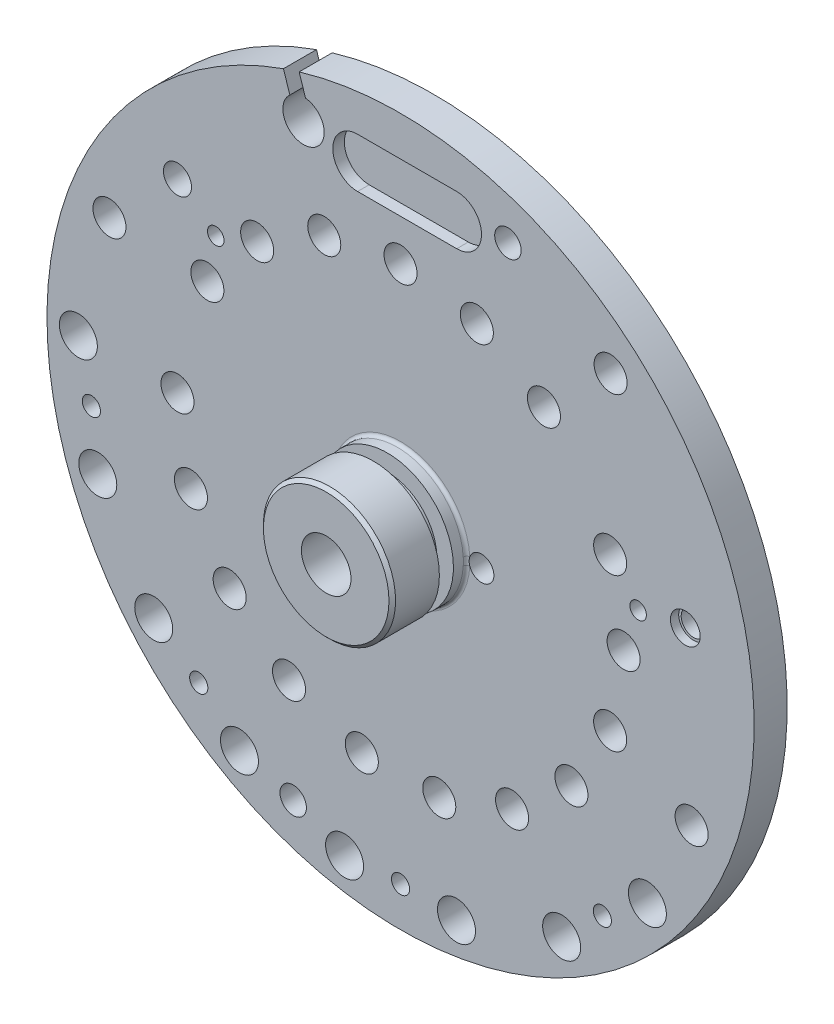
SolidWorks part; units mm, degrees
ref_plane "Front Plane" through (0, 0, 0) normal (0, 0, 1) x (1, 0, 0)
ref_plane "Top Plane" through (0, 0, 0) normal (0, 1, 0) x (1, 0, 0)
ref_plane "Right Plane" through (0, 0, 0) normal (1, 0, 0) x (0, 0, -1)
sketch "Sketch1" plane through (0, 0, 0) normal (0, 0, 1) x (1, 0, 0)
  circle A0 centre (0, 0) radius 21.4
  dimension "D1" = 42.8
extrude "Boss-Extrude1" add sketch "Sketch1" against normal blind 2
sketch "Sketch2" plane through (0, 0, -2) normal (0, 0, -1) x (-1, 0, 0)
  circle A0 centre (0, 0) radius 6.5
  dimension "D1" = 13
extrude "Boss-Extrude2" add sketch "Sketch2" along normal blind 4.7
sketch "Sketch3" plane through (0, 0, 0) normal (0, 0, 1) x (1, 0, 0)
  circle A0 centre (0, 0) radius 4
  dimension "D1" = 8
extrude "Boss-Extrude3" add sketch "Sketch3" along normal offset from surface (4.5 mm away) 6.5 up to face at (6.5, 0, -2)
sketch "Sketch5" plane through (0, 0, -6.7) normal (0, 0, -1) x (-1, 0, 0)
  circle A0 centre (0, 0) radius 3.25
  dimension "D1" = 6.5
extrude "Cut-Extrude2" cut sketch "Sketch5" against normal blind 5.2
sketch "Sketch4" plane through (0, 0, 4.5) normal (0, 0, 1) x (1, 0, 0)
  circle A0 centre (0, 0) radius 1.5
  dimension "D1" = 3
extrude "Cut-Extrude1" cut sketch "Sketch4" against normal up to next
sketch "Sketch6" plane through (0, 0, 0) normal (1, 0, 0) x (0, 0, -1)
  line L0 (-4.5, 0) -> (6.7, 0) construction
  line L1 (-4.5, 4) -> (-4.5, -4) construction
  line L2 (6.7, -6.5) -> (6.7, 6.5) construction
  line L3 (0, 4) -> (-4.5, 4) construction
  line L4 (-1.65, 4) -> (-0.8, 4)
  line L5 (-1.65, 4) -> (-1.65, 3)
  line L6 (-1.65, 3) -> (-0.8, 3)
  line L7 (-0.8, 4) -> (-0.8, 3)
  line L8 (2, -21.4) -> (2, 21.4) construction
  dimension "D1" = 2.8
  dimension "D2" = 0.85
  dimension "D3" = 6
revolve "Cut-Revolve1" cut sketch "Sketch6" angle 360 about L0
sketch "Sketch7" plane through (0, 0, 0) normal (1, 0, 0) x (0, 0, -1)
  line L0 (0, 0) -> (8.4065, 0) construction
  line L1 (6.7, -6.5) -> (6.7, 6.5) construction
  line L2 (6.7, 2.75) -> (6.2, 2.75)
  line L3 (6.7, 2.75) -> (6.7, -2.75)
  line L4 (6.7, -2.75) -> (6.2, -2.75)
  line L5 (6.2, 2.75) -> (6.2, -2.75)
  line L6 (2, -21.4) -> (2, 21.4) construction
  dimension "D1" = 4.2
  dimension "D2" = 5.5
extrude "Cut-Extrude3" cut sketch "Sketch7" against normal through all both and the other way through all
sketch "Sketch8" plane through (0, 0, 0) normal (0, 0, 1) x (1, 0, 0)
  line L0 (0, 0) -> (0, 21.4) construction
  line L1 (-2.6, 17.5) -> (3.4, 17.5) construction
  line L2 (-2.6, 19) -> (3.4, 19)
  line L3 (-2.6, 16) -> (3.4, 16)
  circle A0 centre (0, 0) radius 21.4 construction
  arc A1 (-2.6, 19) -> (-2.6, 16) centre (-2.6, 17.5) ccw
  arc A2 (3.4, 16) -> (3.4, 19) centre (3.4, 17.5) ccw
  circle A3 centre (0, 0) radius 4 construction
  point P7 (0.4, 17.5)
  dimension "D3" = 3
  dimension "D4" = 16
  dimension "D2" = 9
  dimension "D1" = 4.1
extrude "Cut-Extrude4" cut sketch "Sketch8" against normal blind 0.7
hole_wizard "Ø2.0 (2) Diameter Hole6" positions "Sketch14" profile "Sketch13" hole size "Ø2.0" standard "DIN" end condition through all
sketch "Sketch14" plane through (0, 0, -2) normal (0, 0, 1) x (1, 0, 0)
  line L7 (0, 0) -> (-21.4, 0) construction
  line L8 (0, 0) -> (-11.6913, 6.75) construction
  line L9 (-8.6776, 10.3416) -> (0, 0) construction
  line L10 (0, 0) -> (-4.6173, 12.6859) construction
  line L11 (4.6173, 12.6859) -> (0, 0) construction
  line L12 (8.6776, 10.3416) -> (0, 0) construction
  line L13 (0, 0) -> (-12.6859, -4.6173) construction
  line L14 (0, 0) -> (-10.3416, -8.6776) construction
  line L15 (-6.75, -11.6913) -> (0, 0) construction
  line L16 (0, 0) -> (-2.3443, -13.2949) construction
  line L17 (0, 0) -> (2.3443, -13.2949) construction
  line L18 (6.75, -11.6913) -> (0, 0) construction
  line L19 (10.3416, -8.6776) -> (0, 0) construction
  line L20 (12.6859, -4.6173) -> (0, 0) construction
  line L21 (0, 0) -> (13.5, 0) construction
  line L22 (12.6859, 4.6173) -> (0, 0) construction
  circle A1 centre (0, 0) radius 13.5 construction
  circle A2 centre (0, 0) radius 21.4 construction
  point P82 (-11.6913, 6.75)
  point P84 (-8.6776, 10.3416)
  point P86 (-4.6173, 12.6859)
  point P88 (4.6173, 12.6859)
  point P100 (0, 13.5)
  point P103 (8.6776, 10.3416)
  point P108 (-12.6859, -4.6173)
  point P110 (-10.3416, -8.6776)
  point P112 (-6.75, -11.6913)
  point P126 (2.3443, -13.2949)
  point P128 (6.75, -11.6913)
  point P130 (10.3416, -8.6776)
  point P132 (12.6859, -4.6173)
  point P145 (13.5, 0)
  point P147 (12.6859, 4.6173)
  point P156 (-13.5, 0)
  point P159 (-2.3443, -13.2949)
  dimension "D1" = 27
  dimension "D2" = 30
  dimension "D4" = 70
  dimension "D5" = 110
  dimension "D6" = 130
  dimension "D8" = 40
  dimension "D9" = 60
  dimension "D3" = 50
  dimension "D7" = 20
  dimension "D10" = 80
  dimension "D11" = 100
  dimension "D12" = 120
  dimension "D13" = 20
  dimension "D14" = 20
  dimension "D15" = 20
sketch "Sketch13" plane through (-11.6913, 6.75, -2) normal (1, 0, 0) x (0, 1, 0)
  line L0 (0, 0) -> (0, 6.5)
  line L1 (0, 6.5) -> (1, 6.5)
  line L2 (1, 6.5) -> (1, 0)
  line L5 (1, 0) -> (0, 0)
  line L11 (0, -6.35) -> (0, 107.95) construction
  dimension "Thru Hole Dia." = 2
  dimension "Thru Hole Depth" = 6.5
fillet "Fillet2" radius 1 1 edges at (6.5, 0, -2)
hole_wizard "Ø2.3 (2.3) Diameter Hole1" positions "Sketch20" profile "Sketch19" hole size "Ø2.3" standard "DIN" end condition through all
sketch "Sketch20" plane through (0, 0, -2) normal (0, 0, 1) x (1, 0, 0)
  line L3 (0, 0) -> (-19.5, 0) construction
  line L4 (0, 0) -> (-18.324, -6.6694) construction
  line L5 (0, 0) -> (-14.9379, -12.5344) construction
  line L6 (0, 0) -> (-9.75, -16.8875) construction
  line L7 (0, 0) -> (-3.3861, -19.2038) construction
  line L8 (0, 0) -> (3.3861, -19.2038) construction
  line L9 (0, 0) -> (9.75, -16.8875) construction
  line L10 (0, 0) -> (14.9379, -12.5344) construction
  circle A0 centre (0, 0) radius 19.5 construction
  point P35 (-19.5, 0)
  point P60 (-18.324, -6.6694)
  point P66 (-14.9379, -12.5344)
  point P69 (-9.75, -16.8875)
  point P72 (-3.3861, -19.2038)
  point P75 (3.3861, -19.2038)
  point P78 (9.75, -16.8875)
  point P81 (14.9379, -12.5344)
  dimension "D1" = 39
  dimension "D2" = 20
  dimension "D3" = 20
  dimension "D4" = 20
  dimension "D5" = 20
  dimension "D6" = 20
  dimension "D7" = 20
  dimension "D8" = 20
sketch "Sketch19" plane through (-19.5, 0, -2) normal (1, 0, 0) x (0, 1, 0)
  line L0 (0, 0) -> (0, 6.5)
  line L1 (0, 6.5) -> (1.15, 6.5)
  line L2 (1.15, 6.5) -> (1.15, 0)
  line L5 (1.15, 0) -> (0, 0)
  line L11 (0, -6.35) -> (0, 107.95) construction
  dimension "Thru Hole Dia." = 2.3
  dimension "Thru Hole Depth" = 6.5
hole_wizard "Ø2.0 (2) Diameter Hole8" positions "Sketch23" profile "Sketch21" hole size "Ø2.0" standard "DIN" end condition through all
sketch "Sketch23" plane through (0, 0, -2) normal (0, 0, 1) x (1, 0, 0)
  line L0 (0, 0) -> (-21.4, 0) construction
  line L1 (0, 0) -> (-17.6165, 7.1175) construction
  line L2 (12.7135, 14.1198) -> (0, 0) construction
  line L3 (0, 0) -> (17.6165, -7.1175) construction
  circle A0 centre (0, 0) radius 19 construction
  circle A1 centre (0, 0) radius 21.4 construction
  point P11 (-17.6165, 7.1175)
  point P15 (12.7135, 14.1198)
  point P17 (17.6165, -7.1175)
  dimension "D1" = 22
  dimension "D4" = 38
  dimension "D2" = 132
  dimension "D3" = 202
sketch "Sketch21" plane through (-17.6165, 7.1175, -2) normal (1, 0, 0) x (0, 1, 0)
  line L0 (0, 0) -> (0, 6.5)
  line L1 (0, 6.5) -> (1, 6.5)
  line L2 (1, 6.5) -> (1, 0)
  line L5 (1, 0) -> (0, 0)
  line L11 (0, -6.35) -> (0, 107.95) construction
  dimension "Thru Hole Dia." = 2
  dimension "Thru Hole Depth" = 6.5
hole_wizard "Ø2.5 (2.5) Diameter Hole1" positions "Sketch25" profile "Sketch24" hole size "Ø2.5" standard "DIN" end condition through all
sketch "Sketch25" plane through (0, 0, -2) normal (0, 0, 1) x (1, 0, 0)
  line L0 (0, 0) -> (-21.4, 0) construction
  line L1 (-5.8713, 18.0701) -> (0, 0) construction
  line L2 (0, 0) -> (-17.6165, 7.1175) construction
  circle A0 centre (0, 0) radius 19 construction
  circle A1 centre (0, 0) radius 21.4 construction
  point P4 (-5.8713, 18.0701)
  dimension "D1" = 72
sketch "Sketch24" plane through (-5.8713, 18.0701, -2) normal (1, 0, 0) x (0, 1, 0)
  line L0 (0, 0) -> (0, 6.5)
  line L1 (0, 6.5) -> (1.25, 6.5)
  line L2 (1.25, 6.5) -> (1.25, 0)
  line L5 (1.25, 0) -> (0, 0)
  line L11 (0, -6.35) -> (0, 107.95) construction
  dimension "Thru Hole Dia." = 2.5
  dimension "Thru Hole Depth" = 6.5
hole_wizard "Ø1.0 (1) Diameter Hole1" positions "Sketch27" profile "Sketch26" hole size "Ø1.0" standard "DIN" end condition through all
sketch "Sketch27" plane through (0, 0, -2) normal (0, 0, 1) x (1, 0, 0)
  line L0 (0, 0) -> (-21.4, 0) construction
  line L1 (0, 0) -> (14.3782, 2.5353) construction
  line L2 (0, 0) -> (-11.1842, 9.3847) construction
  circle A1 centre (0, 0) radius 14.6 construction
  circle A2 centre (0, 0) radius 21.4 construction
  point P26 (14.3782, 2.5353)
  point P33 (-11.1842, 9.3847)
  dimension "D3" = 29.2
  dimension "D1" = 40
  dimension "D4" = 10
sketch "Sketch26" plane through (14.3782, 2.5353, -2) normal (1, 0, 0) x (0, 1, 0)
  line L0 (0, 0) -> (0, 6.5)
  line L1 (0, 6.5) -> (0.5, 6.5)
  line L2 (0.5, 6.5) -> (0.5, 0)
  line L5 (0.5, 0) -> (0, 0)
  line L11 (0, -6.35) -> (0, 107.95) construction
  dimension "Thru Hole Dia." = 1
  dimension "Thru Hole Depth" = 6.5
hole_wizard "Ø1.7 (1.7) Diameter Hole2" positions "Sketch43" profile "Sketch42" hole size "Ø1.7" standard "DIN" end condition through all
sketch "Sketch43" plane through (0, 0, -2) normal (0, 0, -1) x (-1, 0, 0)
  point P0 (13.5, 11.2)
  dimension "D1" = 13.5
  dimension "D2" = 11.2
sketch "Sketch42" plane through (-13.5, 11.2, -2) normal (1, 0, 0) x (0, 1, 0)
  line L0 (0, 0) -> (0, 6.5)
  line L1 (0, 6.5) -> (0.85, 6.5)
  line L2 (0.85, 6.5) -> (0.85, 0)
  line L5 (0.85, 0) -> (0, 0)
  line L11 (0, -6.35) -> (0, 107.95) construction
  dimension "Thru Hole Dia." = 1.7
  dimension "Thru Hole Depth" = 6.5
hole_wizard "M1.4x0.3 Tapped Hole1" positions "Sketch31" profile "Sketch33" tap size "M1.4x0.3" standard "ANSI Metric" end condition through all
sketch "Sketch31" plane through (0, 0, -2) normal (0, 0, 1) x (1, 0, 0)
  line L0 (0, 0) -> (-18.7113, -3.2993) construction
  line L1 (0, 0) -> (-21.4, 0) construction
  line L2 (0, 0) -> (12.213, -14.5548) construction
  line L3 (0, 0) -> (0, -19) construction
  line L4 (0, 0) -> (-12.213, -14.5548) construction
  circle A0 centre (0, 0) radius 19 construction
  circle A2 centre (0, 0) radius 21.4 construction
  point P22 (-18.7113, -3.2993)
  point P24 (12.213, -14.5548)
  point P26 (-12.213, -14.5548)
  point P28 (0, -19)
  dimension "D1" = 38
  dimension "D2" = 10
  dimension "D3" = 40
  dimension "D4" = 40
sketch "Sketch33" plane through (-18.7113, -3.2993, -2) normal (1, 0, 0) x (0, 1, 0)
  line L0 (0, 0) -> (0, 6.5)
  line L1 (0, 6.5) -> (0.55, 6.5)
  line L2 (0.55, 6.5) -> (0.55, 0)
  line L5 (0.55, 0) -> (0, 0)
  line L11 (0, -6.35) -> (0, 107.95) construction
  dimension "Thru Tap Drill Dia." = 1.1
  dimension "Thru Tap Drill Depth" = 6.5
cosmetic thread "Hole Thread6" parameters "D2"=1.4
cosmetic thread "Hole Thread7" parameters "D2"=1.4
cosmetic thread "Hole Thread8" parameters "D2"=1.4
cosmetic thread "Hole Thread9" parameters "D2"=1.4
hole_wizard "M2 Tapped Hole1" positions "Sketch35" profile "Sketch34" tap size "M2" standard "DIN" end condition through all
sketch "Sketch35" plane through (0, 0, 0) normal (0, 0, 1) x (1, 0, 0)
  line L0 (0, 0) -> (-6.4984, -17.8542) construction
  line L1 (0, 0) -> (0, -21.4) construction
  line L2 (0, 0) -> (0, 21.4) construction
  line L3 (6.4984, 17.8542) -> (0, 0) construction
  circle A0 centre (0, 0) radius 19 construction
  circle A1 centre (0, 0) radius 21.4 construction
  point P28 (6.4984, 17.8542)
  point P30 (-6.4984, -17.8542)
  dimension "D1" = 38
  dimension "D2" = 20
  dimension "D3" = 20
sketch "Sketch34" plane through (6.4984, 17.8542, 0) normal (1, 0, 0) x (0, -1, 0)
  line L0 (0, 0) -> (0, 6.7)
  line L1 (0, 6.7) -> (0.8, 6.7)
  line L2 (0.8, 6.7) -> (0.8, 0)
  line L5 (0.8, 0) -> (0, 0)
  line L11 (0, -6.35) -> (0, 107.95) construction
  dimension "Thru Tap Drill Dia." = 1.6
  dimension "Thru Tap Drill Depth" = 6.7
cosmetic thread "Hole Thread5" parameters "D2"=2
cosmetic thread "Hole Thread10" parameters "D2"=2
hole_wizard "CBORE for M1.7 Hex Socket Head Cap Screw1" positions "Sketch38" profile "Sketch36" counterbore size "M1.6" standard "DIN" end condition through all
sketch "Sketch38" plane through (0, 0, 0) normal (0, 0, 1) x (1, 0, 0)
  line L0 (0, 0) -> (21.4, 0) construction
  line L1 (0, 0) -> (17.2341, 3.0388) construction
  circle A0 centre (0, 0) radius 17.5 construction
  circle A1 centre (0, 0) radius 21.4 construction
  point P0 (17.2341, 3.0388)
  dimension "D1" = 35
  dimension "D2" = 10
sketch "Sketch36" plane through (17.2341, 3.0388, 0) normal (1, 0, 0) x (0, -1, 0)
  line L0 (0, 0) -> (0, 6.7)
  line L1 (0, 6.7) -> (0.75, 6.7)
  line L3 (0.75, 6.7) -> (0.75, 0.5)
  line L4 (0.75, 0.5) -> (0.9, 0.5)
  line L5 (0.9, 0.5) -> (0.9, 0)
  line L7 (0.9, 0) -> (0, 0)
  line L11 (0, -6.35) -> (0, 107.95) construction
  dimension "Thru Hole Dia." = 1.5
  dimension "Thru Hole Depth" = 6.7
  dimension "C'Bore Dia." = 1.8
  dimension "C'Bore Depth" = 0.5
cosmetic thread "Cosmetic Thread1" parameters "D2"=1.7
hole_wizard "CBORE for M1.7 Hex Socket Head Cap Screw2" positions "Sketch40" profile "Sketch39" counterbore size "M1.6" standard "DIN" end condition through all
sketch "Sketch40" plane through (0, 0, -6.2) normal (0, 0, -1) x (-1, 0, 0)
  point P0 (-4.9, 0)
  dimension "D1" = 4.9
sketch "Sketch39" plane through (4.9, 0, -6.2) normal (1, 0, 0) x (0, 1, 0)
  line L0 (0, 0) -> (0, 10.7)
  line L1 (0, 10.7) -> (0.75, 10.7)
  line L3 (0.75, 10.7) -> (0.75, 1.2)
  line L4 (0.75, 1.2) -> (0.9, 1.2)
  line L5 (0.9, 1.2) -> (0.9, 0)
  line L7 (0.9, 0) -> (0, 0)
  line L11 (0, -6.35) -> (0, 107.95) construction
  dimension "Thru Hole Dia." = 1.5
  dimension "Thru Hole Depth" = 10.7
  dimension "C'Bore Dia." = 1.8
  dimension "C'Bore Depth" = 1.2
cosmetic thread "Cosmetic Thread2" parameters "D1"=4.3, "D2"=1.7
sketch "Sketch41" plane through (0, 0, -2) normal (0, 0, 1) x (1, 0, 0)
  line L0 (0, 0) -> (-5.8713, 18.0701) construction
  line L1 (-5.7498, 19.3142) -> (-6.1356, 20.5016)
  line L2 (-6.7009, 19.0051) -> (-7.0867, 20.1925)
  line L3 (-0.4755, -0.1545) -> (-6.3469, 17.9156) construction
  line L4 (0.4755, 0.1545) -> (-5.3958, 18.2246) construction
  circle A0 centre (0, 0) radius 21.4 construction
  arc A1 (-6.1356, 20.5016) -> (-7.0867, 20.1925) centre (0, 0) ccw
  circle A2 centre (-5.8713, 18.0701) radius 1.25 construction
  arc A3 (-5.7498, 19.3142) -> (-6.7009, 19.0051) centre (-5.8713, 18.0701) ccw
  dimension "D1" = 0.5
  dimension "D2" = 0.5
extrude "Cut-Extrude5" cut sketch "Sketch41" along normal through all contours A1 L2 A3 L1
fillet "Fillet3" radius 0.2 1 edges at (4, 0, 0)
chamfer "Chamfer1" distance 0.2 angle 45 1 edges at (4, 0, 4.5)
